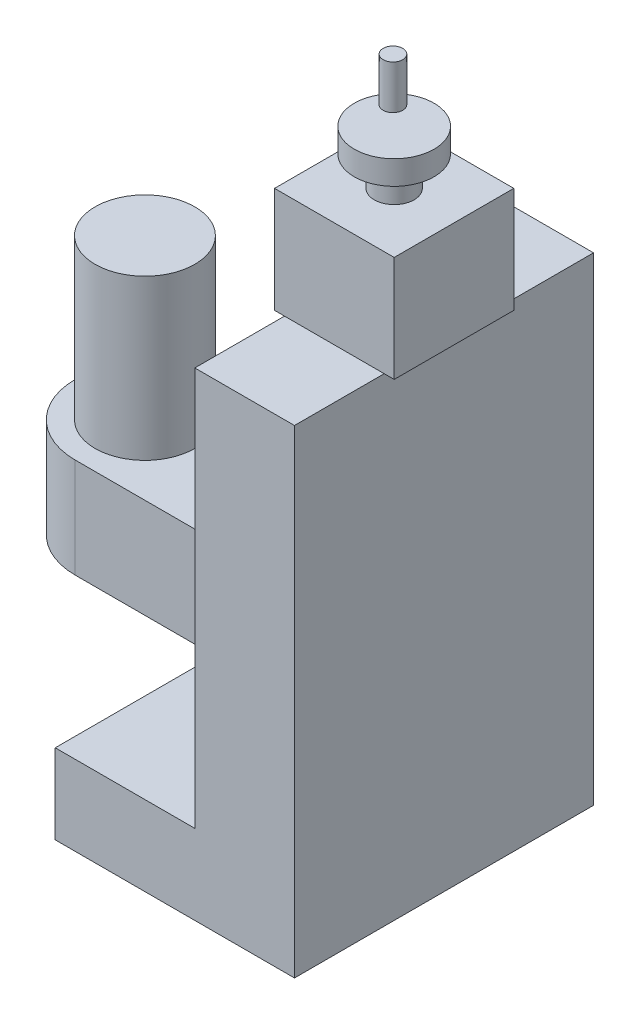
SolidWorks part; units mm, degrees
ref_plane "正面" through (0, 0, 0) normal (0, 0, 1) x (1, 0, 0)
ref_plane "平面" through (0, 0, 0) normal (0, 1, 0) x (1, 0, 0)
ref_plane "右側面" through (0, 0, 0) normal (1, 0, 0) x (0, 0, -1)
sketch "ｽｹｯﾁ1" plane through (0, 0, 0) normal (0, 0, 1) x (1, 0, 0)
  line L1 (0, 0) -> (120, 0)
  line L2 (0, 0) -> (0, 40)
  line L3 (70, 240) -> (120, 240)
  line L4 (120, 0) -> (120, 240)
  line L7 (0, 40) -> (70, 40)
  line L8 (70, 240) -> (70, 40)
  dimension "D1" = 120
  dimension "D2" = 50
  dimension "D3" = 200
  dimension "D4" = 240
extrude "ﾎﾞｽ - 押し出し1" add sketch "ｽｹｯﾁ1" along normal blind 150
sketch "ｽｹｯﾁ2" plane through (70, 0, 0) normal (-1, 0, 0) x (0, 0, 1)
  line L0 (0, 80) -> (150, 80) construction
  line L1 (0, 240) -> (0, 40) construction
  line L2 (150, 240) -> (150, 40) construction
  line L3 (150, 40) -> (0, 40) construction
  dimension "D1" = 40
ref_plane "平面1" through (0, 80, 0) normal (0, 1, 0) x (1, 0, 0)
sketch "ｽｹｯﾁ3" plane through (0, 80, 0) normal (0, 1, 0) x (1, 0, 0)
  line L0 (-25.3957, -75) -> (120, -75) construction
  line L2 (120, -150) -> (120, 0) construction
  line L3 (70, 0) -> (70, -150) construction
  line L4 (70, -40) -> (-30, -40)
  line L5 (70, -40) -> (70, -110)
  line L6 (70, -110) -> (-30, -110)
  line L7 (64.2082, -40) -> (64.2082, -75) construction
  line L8 (64.2082, -75) -> (64.2082, -110) construction
  arc A0 (-30, -40) -> (-30, -110) centre (-30, -75) ccw
  dimension "D2" = 35
  dimension "D3" = 100
extrude "ﾎﾞｽ - 押し出し2" add sketch "ｽｹｯﾁ3" along normal blind 50
sketch "ｽｹｯﾁ4" plane through (0, 130, 0) normal (0, 1, 0) x (1, 0, 0)
  line L0 (-45, -75) -> (70, -75) construction
  line L1 (70, 0) -> (70, -150) construction
  circle A1 centre (-30, -75) radius 25
  dimension "D1" = 50
  dimension "D2" = 100
extrude "ﾎﾞｽ - 押し出し3" add sketch "ｽｹｯﾁ4" along normal blind 80
sketch "ｽｹｯﾁ5" plane through (0, 240, 0) normal (0, 1, 0) x (1, 0, 0)
  line L0 (95, 0) -> (95, -150) construction
  line L1 (120, 0) -> (70, 0) construction
  line L2 (120, -150) -> (70, -150) construction
  line L3 (65, -75) -> (95, -75) construction
  line L4 (65, -45) -> (125, -45)
  line L5 (65, -45) -> (65, -105)
  line L6 (65, -105) -> (125, -105)
  line L7 (125, -45) -> (125, -105)
  line L8 (95, -75) -> (125, -75) construction
  line L9 (100.1125, -45) -> (100.1125, -75) construction
  line L10 (100.1125, -75) -> (100.1125, -105) construction
  dimension "D1" = 30
  dimension "D2" = 30
  dimension "D3" = 45
extrude "ﾎﾞｽ - 押し出し4" add sketch "ｽｹｯﾁ5" along normal blind 53
sketch "ｽｹｯﾁ6" plane through (0, 293, 0) normal (0, 1, 0) x (1, 0, 0)
  line L0 (95, -45) -> (95, -105) construction
  line L1 (125, -45) -> (65, -45) construction
  line L2 (65, -105) -> (125, -105) construction
  line L3 (65, -75) -> (125, -75) construction
  line L4 (65, -45) -> (65, -105) construction
  line L5 (125, -105) -> (125, -45) construction
  circle A0 centre (95, -75) radius 10
  dimension "D1" = 20
extrude "ﾎﾞｽ - 押し出し5" add sketch "ｽｹｯﾁ6" along normal blind 15
sketch "ｽｹｯﾁ7" plane through (0, 308, 0) normal (0, 1, 0) x (1, 0, 0)
  circle A0 centre (95, -75) radius 20
  dimension "D1" = 40
extrude "ﾎﾞｽ - 押し出し6" add sketch "ｽｹｯﾁ7" along normal blind 12
sketch "ｽｹｯﾁ8" plane through (0, 320, 0) normal (0, 1, 0) x (1, 0, 0)
  circle A0 centre (85.3283, -65.953) radius 4.9141
  point P2 (0, 0)
extrude "ﾎﾞｽ - 押し出し7" add sketch "ｽｹｯﾁ8" along normal blind 22
